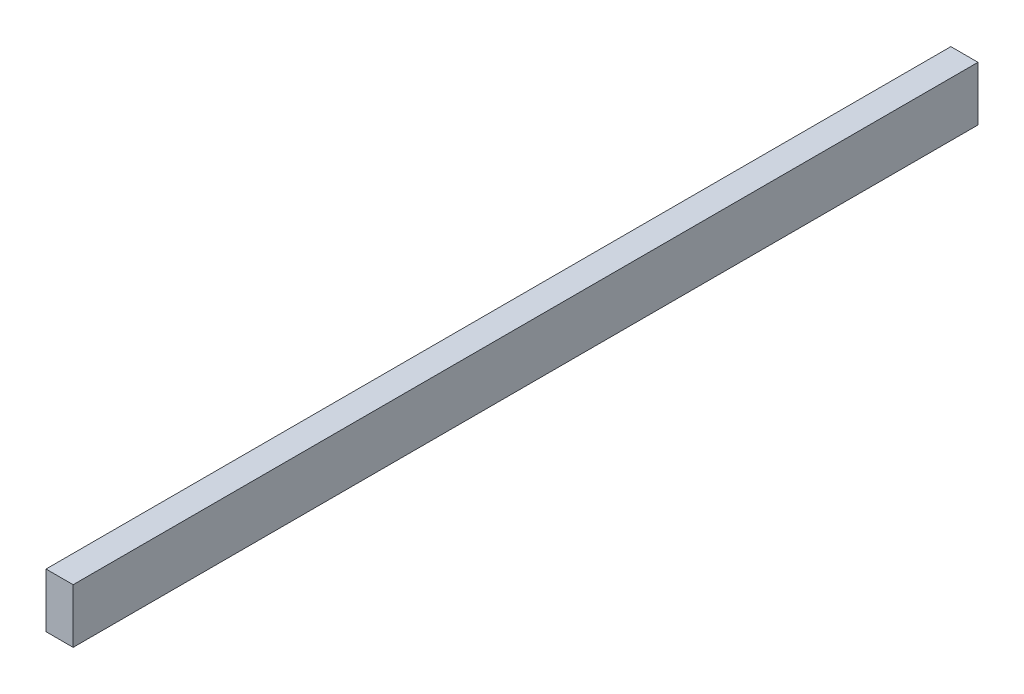
SolidWorks part; units mm, degrees
ref_plane "Front" through (0, 0, 0) normal (0, 0, 1) x (1, 0, 0)
ref_plane "Top" through (0, 0, 0) normal (0, 1, 0) x (1, 0, 0)
ref_plane "Right" through (0, 0, 0) normal (1, 0, 0) x (0, 0, -1)
sketch "草图2" plane through (0, 0, 0) normal (0, 0, 1) x (1, 0, 0)
  line L1 (0, -2.7953) -> (-3, -2.7953)
  line L2 (0, -2.7953) -> (0, 3.2047)
  line L3 (0, 3.2047) -> (-3, 3.2047)
  line L4 (-3, -2.7953) -> (-3, 3.2047)
  dimension "D1" = 3
  dimension "D2" = 6
extrude "凸台-拉伸1" add sketch "草图2" along normal blind 100
